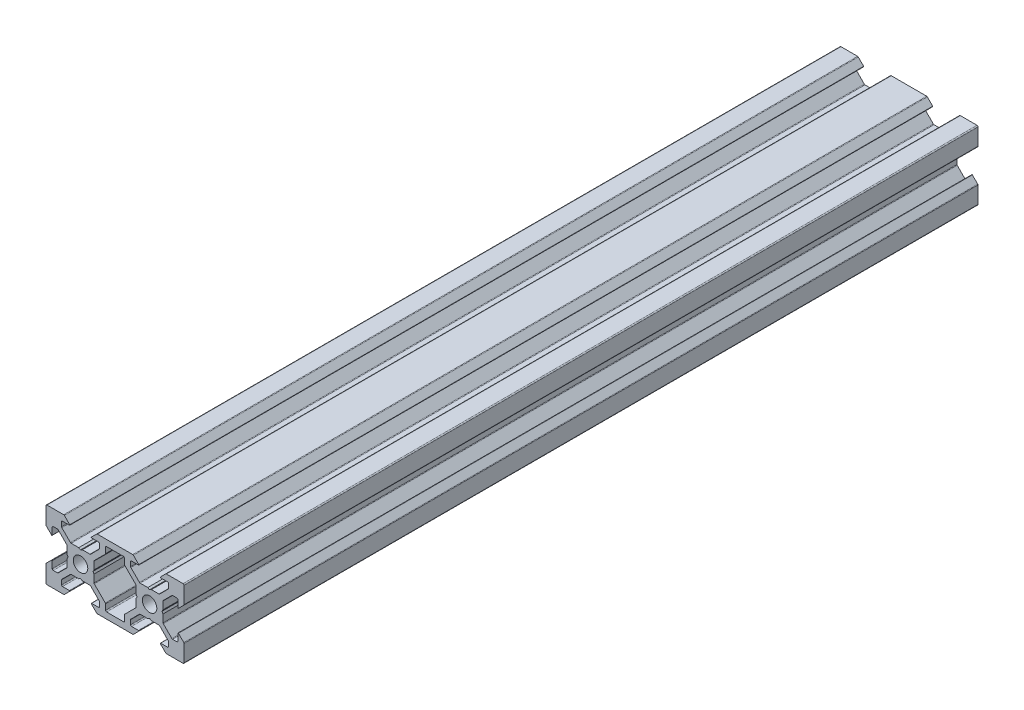
SolidWorks part; units mm, degrees
material "6063-T5"
ref_plane "Plan de face" through (0, 0, 0) normal (0, 0, 1) x (1, 0, 0)
ref_plane "Plan de dessus" through (0, 0, 0) normal (0, 1, 0) x (1, 0, 0)
ref_plane "Plan de droite" through (0, 0, 0) normal (1, 0, 0) x (0, 0, -1)
sketch "Esquisse1" plane through (0, 0, 0) normal (0, 0, 1) x (1, 0, 0)
  line L0 (12.1877, 2.7347) -> (11.6681, 3.0347)
  line L1 (11.6681, 3.0347) -> (9.472, 3.0347)
  line L2 (9.2599, 3.1225) -> (6.7763, 5.6062)
  line L3 (6.6884, 5.8183) -> (6.6884, 7.034)
  line L4 (6.9884, 7.334) -> (8.9877, 7.334)
  line L5 (9.0585, 7.5047) -> (7.517, 9.0462)
  line L6 (7.3049, 9.134) -> (2.1877, 9.134)
  line L7 (2.1877, 9.134) -> (-2.9294, 9.134)
  line L8 (-3.1415, 9.0462) -> (-4.683, 7.5047)
  line L9 (-4.6123, 7.334) -> (-2.6129, 7.334)
  line L10 (-2.3129, 7.034) -> (-2.3129, 5.8183)
  line L11 (-2.4008, 5.6062) -> (-4.8844, 3.1225)
  line L12 (-5.0965, 3.0347) -> (-7.2926, 3.0347)
  line L13 (-7.2926, 3.0347) -> (-7.8123, 2.7347)
  line L14 (-7.8123, 2.7347) -> (-8.3319, 3.0347)
  line L15 (-8.3319, 3.0347) -> (-10.528, 3.0347)
  line L16 (-10.7401, 3.1225) -> (-13.2237, 5.6062)
  line L17 (-13.3116, 5.8183) -> (-13.3116, 7.034)
  line L18 (-13.0116, 7.334) -> (-11.0123, 7.334)
  line L19 (-10.9415, 7.5047) -> (-12.483, 9.0462)
  line L20 (-12.6951, 9.134) -> (-17.5123, 9.134)
  line L21 (-17.8123, 8.834) -> (-17.8123, 4.0169)
  line L22 (-17.7244, 3.8047) -> (-16.183, 2.2633)
  line L23 (-16.0123, 2.334) -> (-16.0123, 4.3334)
  line L24 (-15.7123, 4.6334) -> (-14.4965, 4.6334)
  line L25 (-14.2844, 4.5455) -> (-11.8008, 2.0619)
  line L26 (-11.7129, 1.8498) -> (-11.7129, -0.3464)
  line L27 (-11.7129, -0.3464) -> (-11.4129, -0.866)
  line L28 (-11.4129, -0.866) -> (-11.7129, -1.3856)
  line L29 (-11.7129, -1.3856) -> (-11.7129, -3.5817)
  line L30 (-11.8008, -3.7938) -> (-14.2844, -6.2775)
  line L31 (-14.4965, -6.3653) -> (-15.7123, -6.3653)
  line L32 (-16.0123, -6.0653) -> (-16.0123, -4.066)
  line L33 (-16.183, -3.9953) -> (-17.7244, -5.5367)
  line L34 (-17.8123, -5.7488) -> (-17.8123, -10.566)
  line L35 (-17.5123, -10.866) -> (-12.6951, -10.866)
  line L36 (-12.483, -10.7781) -> (-10.9415, -9.2367)
  line L37 (-11.0123, -9.066) -> (-13.0116, -9.066)
  line L38 (-13.3116, -8.766) -> (-13.3116, -7.5502)
  line L39 (-13.2237, -7.3381) -> (-10.7401, -4.8545)
  line L40 (-10.528, -4.7666) -> (-8.3319, -4.7666)
  line L41 (-8.3319, -4.7666) -> (-7.8123, -4.4666)
  line L42 (-7.8123, -4.4666) -> (-7.2926, -4.7666)
  line L43 (-7.2926, -4.7666) -> (-5.0965, -4.7666)
  line L44 (-4.8844, -4.8545) -> (-2.4008, -7.3381)
  line L45 (-2.3129, -7.5502) -> (-2.3129, -8.766)
  line L46 (-2.6129, -9.066) -> (-4.6123, -9.066)
  line L47 (-4.683, -9.2367) -> (-3.1415, -10.7781)
  line L48 (-2.9294, -10.866) -> (2.1877, -10.866)
  line L49 (2.1877, -10.866) -> (7.3049, -10.866)
  line L50 (7.517, -10.7781) -> (9.0585, -9.2367)
  line L51 (8.9877, -9.066) -> (6.9884, -9.066)
  line L52 (6.6884, -8.766) -> (6.6884, -7.5502)
  line L53 (6.7763, -7.3381) -> (9.2599, -4.8545)
  line L54 (9.472, -4.7666) -> (11.6681, -4.7666)
  line L55 (11.6681, -4.7666) -> (12.1877, -4.4666)
  line L56 (12.1877, -4.4666) -> (12.7074, -4.7666)
  line L57 (12.7074, -4.7666) -> (14.9035, -4.7666)
  line L58 (15.1156, -4.8545) -> (17.5992, -7.3381)
  line L59 (17.6871, -7.5502) -> (17.6871, -8.766)
  line L60 (17.3871, -9.066) -> (15.3877, -9.066)
  line L61 (15.317, -9.2367) -> (16.8585, -10.7781)
  line L62 (17.0706, -10.866) -> (21.8877, -10.866)
  line L63 (22.1877, -10.566) -> (22.1877, -5.7488)
  line L64 (22.0999, -5.5367) -> (20.5585, -3.9953)
  line L65 (20.3877, -4.066) -> (20.3877, -6.0653)
  line L66 (20.0877, -6.3653) -> (18.872, -6.3653)
  line L67 (18.6599, -6.2775) -> (16.1763, -3.7938)
  line L68 (16.0884, -3.5817) -> (16.0884, -1.3856)
  line L69 (16.0884, -1.3856) -> (15.7884, -0.866)
  line L70 (15.7884, -0.866) -> (16.0884, -0.3464)
  line L71 (16.0884, -0.3464) -> (16.0884, 1.8498)
  line L72 (16.1763, 2.0619) -> (18.6599, 4.5455)
  line L73 (18.872, 4.6334) -> (20.0877, 4.6334)
  line L74 (20.3877, 4.3334) -> (20.3877, 2.334)
  line L75 (20.5585, 2.2633) -> (22.0999, 3.8047)
  line L76 (22.1877, 4.0169) -> (22.1877, 8.834)
  line L77 (21.8877, 9.134) -> (17.0706, 9.134)
  line L78 (16.8585, 9.0462) -> (15.317, 7.5047)
  line L79 (15.3877, 7.334) -> (17.3871, 7.334)
  line L80 (17.6871, 7.034) -> (17.6871, 5.8183)
  line L81 (17.5992, 5.6062) -> (15.1156, 3.1225)
  line L82 (14.9035, 3.0347) -> (12.7074, 3.0347)
  line L83 (12.7074, 3.0347) -> (12.1877, 2.7347)
  line L180 (4.9271, -8.766) -> (4.9271, -7.1902)
  line L181 (5.015, -6.9781) -> (8.1992, -3.7938)
  line L182 (8.2871, -3.5817) -> (8.2871, -1.3856)
  line L183 (8.2871, -1.3856) -> (8.5871, -0.866)
  line L184 (8.5871, -0.866) -> (8.2871, -0.3464)
  line L185 (8.2871, -0.3464) -> (8.2871, 1.8498)
  line L186 (8.1992, 2.0619) -> (5.015, 5.2462)
  line L187 (4.9271, 5.4583) -> (4.9271, 7.034)
  line L188 (4.6271, 7.334) -> (2.1877, 7.334)
  line L189 (2.1877, 7.334) -> (-0.2516, 7.334)
  line L190 (-0.5516, 7.034) -> (-0.5516, 5.4583)
  line L191 (-0.6395, 5.2462) -> (-3.8237, 2.0619)
  line L192 (-3.9116, 1.8498) -> (-3.9116, -0.3464)
  line L193 (-3.9116, -0.3464) -> (-4.2116, -0.866)
  line L194 (-4.2116, -0.866) -> (-3.9116, -1.3856)
  line L195 (-3.9116, -1.3856) -> (-3.9116, -3.5817)
  line L196 (-3.8237, -3.7938) -> (-0.6395, -6.9781)
  line L197 (-0.5516, -7.1902) -> (-0.5516, -8.766)
  line L198 (-0.2516, -9.066) -> (2.1877, -9.066)
  line L199 (2.1877, -9.066) -> (4.6271, -9.066)
  arc A0 (-7.8123, 1.234) -> (-9.9123, -0.866) centre (-7.8123, -0.866) ccw
  arc A1 (-9.9123, -0.866) -> (-7.8123, -2.966) centre (-7.8123, -0.866) ccw
  arc A2 (-7.8123, -2.966) -> (-5.7123, -0.866) centre (-7.8123, -0.866) ccw
  arc A3 (-5.7123, -0.866) -> (-7.8123, 1.234) centre (-7.8123, -0.866) ccw
  arc A4 (12.1877, 1.234) -> (10.0877, -0.866) centre (12.1877, -0.866) ccw
  arc A5 (10.0877, -0.866) -> (12.1877, -2.966) centre (12.1877, -0.866) ccw
  arc A6 (12.1877, -2.966) -> (14.2877, -0.866) centre (12.1877, -0.866) ccw
  arc A7 (14.2877, -0.866) -> (12.1877, 1.234) centre (12.1877, -0.866) ccw
  arc A8 (9.2599, 3.1225) -> (9.472, 3.0347) centre (9.472, 3.3347) ccw
  arc A9 (6.6884, 5.8183) -> (6.7763, 5.6062) centre (6.9884, 5.8183) ccw
  arc A10 (6.9884, 7.334) -> (6.6884, 7.034) centre (6.9884, 7.034) ccw
  arc A11 (8.9877, 7.334) -> (9.0585, 7.5047) centre (8.9877, 7.434) ccw
  arc A12 (7.517, 9.0462) -> (7.3049, 9.134) centre (7.3049, 8.834) ccw
  arc A13 (-2.9294, 9.134) -> (-3.1415, 9.0462) centre (-2.9294, 8.834) ccw
  arc A14 (-4.683, 7.5047) -> (-4.6123, 7.334) centre (-4.6123, 7.434) ccw
  arc A15 (-2.3129, 7.034) -> (-2.6129, 7.334) centre (-2.6129, 7.034) ccw
  arc A16 (-2.4008, 5.6062) -> (-2.3129, 5.8183) centre (-2.6129, 5.8183) ccw
  arc A17 (-5.0965, 3.0347) -> (-4.8844, 3.1225) centre (-5.0965, 3.3347) ccw
  arc A18 (-10.7401, 3.1225) -> (-10.528, 3.0347) centre (-10.528, 3.3347) ccw
  arc A19 (-13.3116, 5.8183) -> (-13.2237, 5.6062) centre (-13.0116, 5.8183) ccw
  arc A20 (-13.0116, 7.334) -> (-13.3116, 7.034) centre (-13.0116, 7.034) ccw
  arc A21 (-11.0123, 7.334) -> (-10.9415, 7.5047) centre (-11.0123, 7.434) ccw
  arc A22 (-12.483, 9.0462) -> (-12.6951, 9.134) centre (-12.6951, 8.834) ccw
  arc A23 (-17.5123, 9.134) -> (-17.8123, 8.834) centre (-17.5123, 8.834) ccw
  arc A24 (-17.8123, 4.0169) -> (-17.7244, 3.8047) centre (-17.5123, 4.0169) ccw
  arc A25 (-16.183, 2.2633) -> (-16.0123, 2.334) centre (-16.1123, 2.334) ccw
  arc A26 (-15.7123, 4.6334) -> (-16.0123, 4.3334) centre (-15.7123, 4.3334) ccw
  arc A27 (-14.2844, 4.5455) -> (-14.4965, 4.6334) centre (-14.4965, 4.3334) ccw
  arc A28 (-11.7129, 1.8498) -> (-11.8008, 2.0619) centre (-12.0129, 1.8498) ccw
  arc A29 (-11.8008, -3.7938) -> (-11.7129, -3.5817) centre (-12.0129, -3.5817) ccw
  arc A30 (-14.4965, -6.3653) -> (-14.2844, -6.2775) centre (-14.4965, -6.0653) ccw
  arc A31 (-16.0123, -6.0653) -> (-15.7123, -6.3653) centre (-15.7123, -6.0653) ccw
  arc A32 (-16.0123, -4.066) -> (-16.183, -3.9953) centre (-16.1123, -4.066) ccw
  arc A33 (-17.7244, -5.5367) -> (-17.8123, -5.7488) centre (-17.5123, -5.7488) ccw
  arc A34 (-17.8123, -10.566) -> (-17.5123, -10.866) centre (-17.5123, -10.566) ccw
  arc A35 (-12.6951, -10.866) -> (-12.483, -10.7781) centre (-12.6951, -10.566) ccw
  arc A36 (-10.9415, -9.2367) -> (-11.0123, -9.066) centre (-11.0123, -9.166) ccw
  arc A37 (-13.3116, -8.766) -> (-13.0116, -9.066) centre (-13.0116, -8.766) ccw
  arc A38 (-13.2237, -7.3381) -> (-13.3116, -7.5502) centre (-13.0116, -7.5502) ccw
  arc A39 (-10.528, -4.7666) -> (-10.7401, -4.8545) centre (-10.528, -5.0666) ccw
  arc A40 (-4.8844, -4.8545) -> (-5.0965, -4.7666) centre (-5.0965, -5.0666) ccw
  arc A41 (-2.3129, -7.5502) -> (-2.4008, -7.3381) centre (-2.6129, -7.5502) ccw
  arc A42 (-2.6129, -9.066) -> (-2.3129, -8.766) centre (-2.6129, -8.766) ccw
  arc A43 (-4.6123, -9.066) -> (-4.683, -9.2367) centre (-4.6123, -9.166) ccw
  arc A44 (-3.1415, -10.7781) -> (-2.9294, -10.866) centre (-2.9294, -10.566) ccw
  arc A45 (7.3049, -10.866) -> (7.517, -10.7781) centre (7.3049, -10.566) ccw
  arc A46 (9.0585, -9.2367) -> (8.9877, -9.066) centre (8.9877, -9.166) ccw
  arc A47 (6.6884, -8.766) -> (6.9884, -9.066) centre (6.9884, -8.766) ccw
  arc A48 (6.7763, -7.3381) -> (6.6884, -7.5502) centre (6.9884, -7.5502) ccw
  arc A49 (9.472, -4.7666) -> (9.2599, -4.8545) centre (9.472, -5.0666) ccw
  arc A50 (15.1156, -4.8545) -> (14.9035, -4.7666) centre (14.9035, -5.0666) ccw
  arc A51 (17.6871, -7.5502) -> (17.5992, -7.3381) centre (17.3871, -7.5502) ccw
  arc A52 (17.3871, -9.066) -> (17.6871, -8.766) centre (17.3871, -8.766) ccw
  arc A53 (15.3877, -9.066) -> (15.317, -9.2367) centre (15.3877, -9.166) ccw
  arc A54 (16.8585, -10.7781) -> (17.0706, -10.866) centre (17.0706, -10.566) ccw
  arc A55 (21.8877, -10.866) -> (22.1877, -10.566) centre (21.8877, -10.566) ccw
  arc A56 (22.1877, -5.7488) -> (22.0999, -5.5367) centre (21.8877, -5.7488) ccw
  arc A57 (20.5585, -3.9953) -> (20.3877, -4.066) centre (20.4877, -4.066) ccw
  arc A58 (20.0877, -6.3653) -> (20.3877, -6.0653) centre (20.0877, -6.0653) ccw
  arc A59 (18.6599, -6.2775) -> (18.872, -6.3653) centre (18.872, -6.0653) ccw
  arc A60 (16.0884, -3.5817) -> (16.1763, -3.7938) centre (16.3884, -3.5817) ccw
  arc A61 (16.1763, 2.0619) -> (16.0884, 1.8498) centre (16.3884, 1.8498) ccw
  arc A62 (18.872, 4.6334) -> (18.6599, 4.5455) centre (18.872, 4.3334) ccw
  arc A63 (20.3877, 4.3334) -> (20.0877, 4.6334) centre (20.0877, 4.3334) ccw
  arc A64 (20.3877, 2.334) -> (20.5585, 2.2633) centre (20.4877, 2.334) ccw
  arc A65 (22.0999, 3.8047) -> (22.1877, 4.0169) centre (21.8877, 4.0169) ccw
  arc A66 (22.1877, 8.834) -> (21.8877, 9.134) centre (21.8877, 8.834) ccw
  arc A67 (17.0706, 9.134) -> (16.8585, 9.0462) centre (17.0706, 8.834) ccw
  arc A68 (15.317, 7.5047) -> (15.3877, 7.334) centre (15.3877, 7.434) ccw
  arc A69 (17.6871, 7.034) -> (17.3871, 7.334) centre (17.3871, 7.034) ccw
  arc A70 (17.5992, 5.6062) -> (17.6871, 5.8183) centre (17.3871, 5.8183) ccw
  arc A71 (14.9035, 3.0347) -> (15.1156, 3.1225) centre (14.9035, 3.3347) ccw
  arc A130 (4.6271, -9.066) -> (4.9271, -8.766) centre (4.6271, -8.766) ccw
  arc A131 (5.015, -6.9781) -> (4.9271, -7.1902) centre (5.2271, -7.1902) ccw
  arc A132 (8.1992, -3.7938) -> (8.2871, -3.5817) centre (7.9871, -3.5817) ccw
  arc A133 (8.2871, 1.8498) -> (8.1992, 2.0619) centre (7.9871, 1.8498) ccw
  arc A134 (4.9271, 5.4583) -> (5.015, 5.2462) centre (5.2271, 5.4583) ccw
  arc A135 (4.9271, 7.034) -> (4.6271, 7.334) centre (4.6271, 7.034) ccw
  arc A136 (-0.2516, 7.334) -> (-0.5516, 7.034) centre (-0.2516, 7.034) ccw
  arc A137 (-0.6395, 5.2462) -> (-0.5516, 5.4583) centre (-0.8516, 5.4583) ccw
  arc A138 (-3.8237, 2.0619) -> (-3.9116, 1.8498) centre (-3.6116, 1.8498) ccw
  arc A139 (-3.9116, -3.5817) -> (-3.8237, -3.7938) centre (-3.6116, -3.5817) ccw
  arc A140 (-0.5516, -7.1902) -> (-0.6395, -6.9781) centre (-0.8516, -7.1902) ccw
  arc A141 (-0.5516, -8.766) -> (-0.2516, -9.066) centre (-0.2516, -8.766) ccw
extrude "Boss.-Extru.2" add sketch "Esquisse1" along normal blind 230
